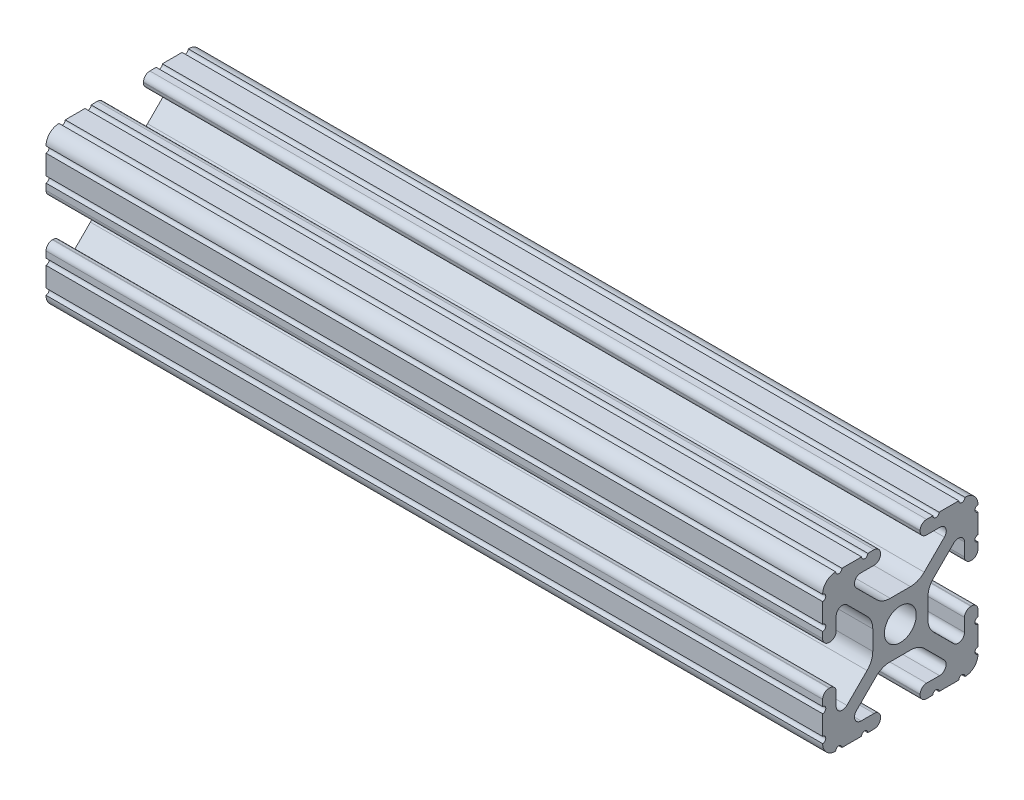
SolidWorks part; units mm, degrees
material "6061-T6 (SS)"
ref_plane "Front Plane" through (0, 0, 0) normal (0, 0, 1) x (1, 0, 0)
ref_plane "Top Plane" through (0, 0, 0) normal (0, 1, 0) x (1, 0, 0)
ref_plane "Right Plane" through (0, 0, 0) normal (1, 0, 0) x (0, 0, -1)
sketch "Sketch1" plane through (0, 0, 0) normal (1, 0, 0) x (0, 0, -1)
  line L0 (6.3331, -12.7) -> (9.5504, -12.7)
  line L1 (12.7, -9.5504) -> (12.7, -6.3331)
  line L2 (12.7, -5.3171) -> (12.7, -4.2875)
  line L3 (11.651, -3.2385) -> (11.5392, -3.2385)
  line L4 (10.4902, -4.2875) -> (10.4902, -6.4021)
  line L5 (8.7371, -7.1294) -> (5.441, -3.8408)
  line L6 (4.5085, -1.5932) -> (4.5085, 1.5932)
  line L7 (5.441, 3.8408) -> (8.7371, 7.1294)
  line L8 (10.4902, 6.4021) -> (10.4902, 4.2875)
  line L9 (11.5392, 3.2385) -> (11.651, 3.2385)
  line L10 (12.7, 4.2875) -> (12.7, 5.3171)
  line L11 (12.7, 6.3331) -> (12.7, 9.5504)
  line L12 (9.5504, 12.7) -> (6.3331, 12.7)
  line L13 (5.3171, 12.7) -> (4.2875, 12.7)
  line L14 (3.2385, 11.651) -> (3.2385, 11.5392)
  line L15 (4.2875, 10.4902) -> (6.4768, 10.4902)
  line L16 (7.207, 8.7244) -> (3.8983, 5.4232)
  line L17 (1.6558, 4.4958) -> (-1.6558, 4.4958)
  line L18 (-3.8983, 5.4232) -> (-7.207, 8.7244)
  line L19 (-6.4768, 10.4902) -> (-4.2875, 10.4902)
  line L20 (-3.2385, 11.5392) -> (-3.2385, 11.651)
  line L21 (-4.2875, 12.7) -> (-5.3171, 12.7)
  line L22 (-6.3331, 12.7) -> (-9.5504, 12.7)
  line L23 (-12.7, 9.5504) -> (-12.7, 6.3331)
  line L24 (-12.7, 5.3171) -> (-12.7, 4.2875)
  line L25 (-11.651, 3.2385) -> (-11.5392, 3.2385)
  line L26 (-10.4902, 4.2875) -> (-10.4902, 6.4021)
  line L27 (-8.7371, 7.1294) -> (-5.441, 3.8408)
  line L28 (-4.5085, 1.5932) -> (-4.5085, -1.5932)
  line L29 (-5.441, -3.8408) -> (-8.7371, -7.1294)
  line L30 (-10.4902, -6.4021) -> (-10.4902, -4.2875)
  line L31 (-11.5392, -3.2385) -> (-11.651, -3.2385)
  line L32 (-12.7, -4.2875) -> (-12.7, -5.3171)
  line L33 (-12.7, -6.3331) -> (-12.7, -9.5504)
  line L34 (-9.5504, -12.7) -> (-6.3331, -12.7)
  line L35 (-5.3171, -12.7) -> (-4.2875, -12.7)
  line L36 (-3.2385, -11.651) -> (-3.2385, -11.5392)
  line L37 (-4.2875, -10.4902) -> (-6.4164, -10.4902)
  line L38 (-7.1797, -8.6452) -> (-3.9523, -5.4237)
  line L39 (-1.7093, -4.4958) -> (1.7093, -4.4958)
  line L40 (3.9523, -5.4237) -> (7.1797, -8.6452)
  line L41 (6.4164, -10.4902) -> (4.2875, -10.4902)
  line L42 (3.2385, -11.5392) -> (3.2385, -11.651)
  line L43 (4.2875, -12.7) -> (5.3171, -12.7)
  circle A0 centre (0, 0) radius 2.6035
  arc A1 (6.3331, -12.7) -> (5.3171, -12.7) centre (5.8251, -12.7) ccw
  arc A2 (10.5664, -12.6998) -> (9.5504, -12.7) centre (10.0584, -12.7) ccw
  arc A3 (10.5664, -12.6998) -> (12.6998, -10.5664) centre (10.5918, -10.5918) ccw
  arc A4 (12.7, -9.5504) -> (12.6998, -10.5664) centre (12.7, -10.0584) ccw
  arc A5 (12.7, -5.3171) -> (12.7, -6.3331) centre (12.7, -5.8251) ccw
  arc A6 (12.7, -4.2875) -> (11.651, -3.2385) centre (11.651, -4.2875) ccw
  arc A7 (11.5392, -3.2385) -> (10.4902, -4.2875) centre (11.5392, -4.2875) ccw
  arc A8 (8.7371, -7.1294) -> (10.4902, -6.4021) centre (9.4628, -6.4021) ccw
  arc A9 (5.441, 3.8408) -> (4.5085, 1.5932) centre (7.6835, 1.5932) ccw
  arc A10 (10.4902, 6.4021) -> (8.7371, 7.1294) centre (9.4628, 6.4021) ccw
  arc A11 (10.4902, 4.2875) -> (11.5392, 3.2385) centre (11.5392, 4.2875) ccw
  arc A12 (11.651, 3.2385) -> (12.7, 4.2875) centre (11.651, 4.2875) ccw
  arc A13 (12.7, 6.3331) -> (12.7, 5.3171) centre (12.7, 5.8251) ccw
  arc A14 (12.6998, 10.5664) -> (12.7, 9.5504) centre (12.7, 10.0584) ccw
  arc A15 (12.6998, 10.5664) -> (10.5664, 12.6998) centre (10.5918, 10.5918) ccw
  arc A16 (9.5504, 12.7) -> (10.5664, 12.6998) centre (10.0584, 12.7) ccw
  arc A17 (5.3171, 12.7) -> (6.3331, 12.7) centre (5.8251, 12.7) ccw
  arc A18 (4.2875, 12.7) -> (3.2385, 11.651) centre (4.2875, 11.651) ccw
  arc A19 (3.2385, 11.5392) -> (4.2875, 10.4902) centre (4.2875, 11.5392) ccw
  arc A20 (7.207, 8.7244) -> (6.4768, 10.4902) centre (6.4768, 9.4563) ccw
  arc A21 (1.6558, 4.4958) -> (3.8983, 5.4232) centre (1.6558, 7.6708) ccw
  arc A22 (-3.8983, 5.4232) -> (-1.6558, 4.4958) centre (-1.6558, 7.6708) ccw
  arc A23 (-6.4768, 10.4902) -> (-7.207, 8.7244) centre (-6.4768, 9.4563) ccw
  arc A24 (-4.2875, 10.4902) -> (-3.2385, 11.5392) centre (-4.2875, 11.5392) ccw
  arc A25 (-3.2385, 11.651) -> (-4.2875, 12.7) centre (-4.2875, 11.651) ccw
  arc A26 (-6.3331, 12.7) -> (-5.3171, 12.7) centre (-5.8251, 12.7) ccw
  arc A27 (-10.5664, 12.6998) -> (-9.5504, 12.7) centre (-10.0584, 12.7) ccw
  arc A28 (-10.5664, 12.6998) -> (-12.6998, 10.5664) centre (-10.5918, 10.5918) ccw
  arc A29 (-12.7, 9.5504) -> (-12.6998, 10.5664) centre (-12.7, 10.0584) ccw
  arc A30 (-12.7, 5.3171) -> (-12.7, 6.3331) centre (-12.7, 5.8251) ccw
  arc A31 (-12.7, 4.2875) -> (-11.651, 3.2385) centre (-11.651, 4.2875) ccw
  arc A32 (-11.5392, 3.2385) -> (-10.4902, 4.2875) centre (-11.5392, 4.2875) ccw
  arc A33 (-8.7371, 7.1294) -> (-10.4902, 6.4021) centre (-9.4628, 6.4021) ccw
  arc A34 (-4.5085, 1.5932) -> (-5.441, 3.8408) centre (-7.6835, 1.5932) ccw
  arc A35 (-5.441, -3.8408) -> (-4.5085, -1.5932) centre (-7.6835, -1.5932) ccw
  arc A36 (-10.4902, -6.4021) -> (-8.7371, -7.1294) centre (-9.4628, -6.4021) ccw
  arc A37 (-10.4902, -4.2875) -> (-11.5392, -3.2385) centre (-11.5392, -4.2875) ccw
  arc A38 (-11.651, -3.2385) -> (-12.7, -4.2875) centre (-11.651, -4.2875) ccw
  arc A39 (-12.7, -6.3331) -> (-12.7, -5.3171) centre (-12.7, -5.8251) ccw
  arc A40 (-12.6998, -10.5664) -> (-12.7, -9.5504) centre (-12.7, -10.0584) ccw
  arc A41 (-12.6998, -10.5664) -> (-10.5664, -12.6998) centre (-10.5918, -10.5918) ccw
  arc A42 (-9.5504, -12.7) -> (-10.5664, -12.6998) centre (-10.0584, -12.7) ccw
  arc A43 (-5.3171, -12.7) -> (-6.3331, -12.7) centre (-5.8251, -12.7) ccw
  arc A44 (-4.2875, -12.7) -> (-3.2385, -11.651) centre (-4.2875, -11.651) ccw
  arc A45 (-3.2385, -11.5392) -> (-4.2875, -10.4902) centre (-4.2875, -11.5392) ccw
  arc A46 (-7.1797, -8.6452) -> (-6.4164, -10.4902) centre (-6.4164, -9.4098) ccw
  arc A47 (-1.7093, -4.4958) -> (-3.9523, -5.4237) centre (-1.7093, -7.6708) ccw
  arc A48 (3.9523, -5.4237) -> (1.7093, -4.4958) centre (1.7093, -7.6708) ccw
  arc A49 (6.4164, -10.4902) -> (7.1797, -8.6452) centre (6.4164, -9.4098) ccw
  arc A50 (4.2875, -10.4902) -> (3.2385, -11.5392) centre (4.2875, -11.5392) ccw
  arc A51 (3.2385, -11.651) -> (4.2875, -12.7) centre (4.2875, -11.651) ccw
  arc A52 (5.441, -3.8408) -> (4.5085, -1.5932) centre (7.6835, -1.5932) cw
  dimension "D1" = 3.175
extrude "Boss-Extrude1" add sketch "Sketch1" along normal mid plane 127
